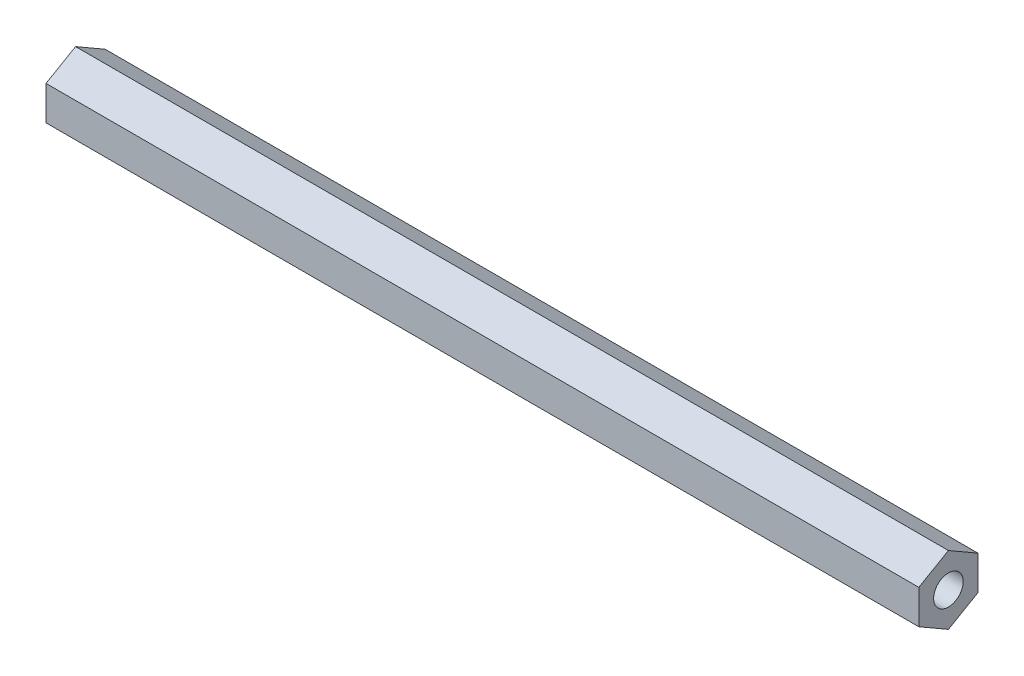
SolidWorks part; units mm, degrees
ref_plane "Front Plane" through (0, 0, 0) normal (0, 0, 1) x (1, 0, 0)
ref_plane "Top Plane" through (0, 0, 0) normal (0, 1, 0) x (1, 0, 0)
ref_plane "Right Plane" through (0, 0, 0) normal (1, 0, 0) x (0, 0, -1)
sketch "Sketch1" plane through (0, 0, 0) normal (1, 0, 0) x (0, 0, -1)
  line L1 (0, 7.3323) -> (-6.35, 3.6662)
  line L2 (-6.35, 3.6662) -> (-6.35, -3.6662)
  line L3 (-6.35, -3.6662) -> (0, -7.3323)
  line L4 (0, -7.3323) -> (6.35, -3.6662)
  line L5 (6.35, -3.6662) -> (6.35, 3.6662)
  line L6 (6.35, 3.6662) -> (0, 7.3323)
  circle A0 centre (0, 0) radius 6.35 construction
  circle A1 centre (0, 0) radius 3.175
  dimension "D2" = 6.35
  dimension "D1" = 12.7
extrude "Boss-Extrude1" add sketch "Sketch1" along normal blind 187.325
